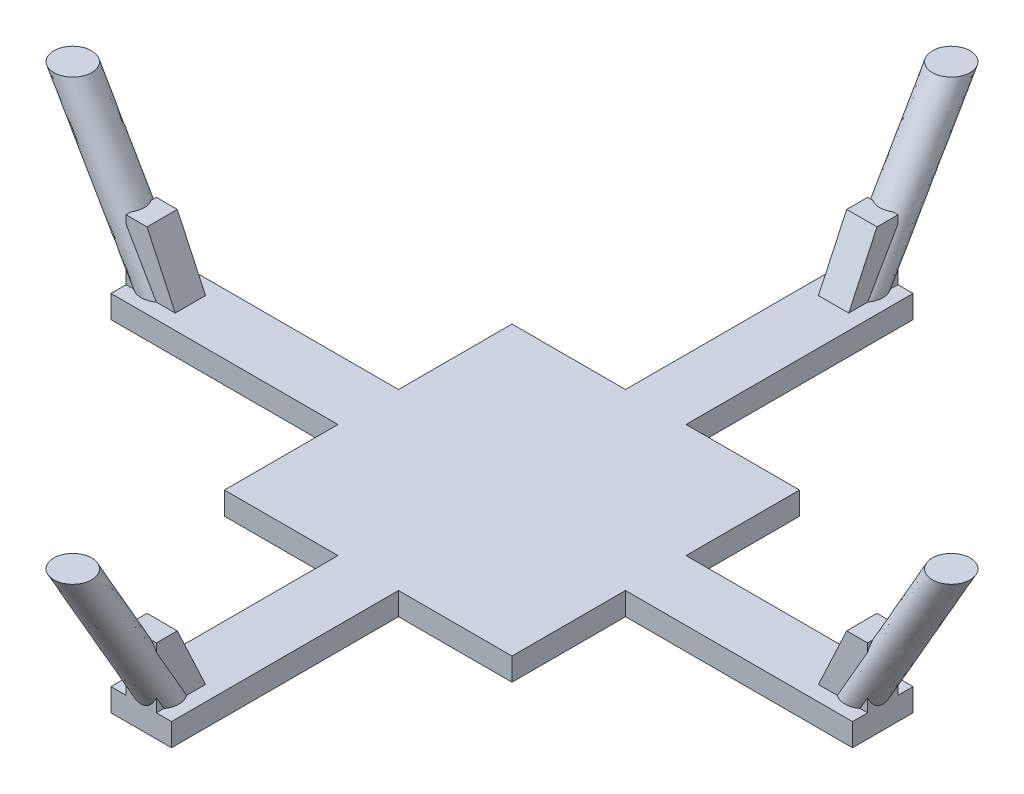
SolidWorks part; units mm, degrees
ref_plane "Front Plane" through (0, 0, 0) normal (0, 0, 1) x (1, 0, 0)
ref_plane "Top Plane" through (0, 0, 0) normal (0, 1, 0) x (1, 0, 0)
ref_plane "Right Plane" through (0, 0, 0) normal (1, 0, 0) x (0, 0, -1)
sketch "Sketch1" plane through (0, 0, 0) normal (0, 1, 0) x (1, 0, 0)
  line L1 (19, -19) -> (-19, -19)
  line L2 (19, -19) -> (19, 19)
  line L3 (19, 19) -> (-19, 19)
  line L4 (-19, -19) -> (-19, 19)
  line L5 (19, -19) -> (-19, 19) construction
  line L6 (19, 19) -> (-19, -19) construction
  point P0 (0, 0)
  dimension "D1" = 38
extrude "Boss-Extrude1" add sketch "Sketch1" along normal blind 3
sketch "Sketch2" plane through (0, 0, 0) normal (0, 1, 0) x (1, 0, 0)
  line L0 (-19, 4) -> (-49, 4)
  line L1 (-19, 19) -> (-19, -19) construction
  line L2 (-49, 4) -> (-49, -4)
  line L3 (-49, -4) -> (-19, -4)
  line L4 (-19, 0) -> (-49, 0) construction
  line L5 (-19, 4) -> (-19, -4)
  dimension "D1" = 8
  dimension "D2" = 30
extrude "Boss-Extrude2" add sketch "Sketch2" along normal up to surface (3 mm away) up to face at (0, 3, 0)
ref_axis "Axis1" through (0, 0, 0) along (0, 1, 0)
sketch "Sketch3" plane through (0, 3, 0) normal (0, 1, 0) x (1, 0, 0)
  line L0 (-49, 4) -> (-49, -4) construction
  line L1 (0, 0) -> (-46.5, 0) construction
  circle A0 centre (-46.5, 0) radius 2.5
  dimension "D1" = 5
extrude "Boss-Extrude3" [suppressed] add sketch "Sketch3" along normal blind 20
sketch "Sketch7" plane through (0, 0, 0) normal (0, 0, 1) x (1, 0, 0)
  line L0 (-46.5, 23) -> (-46.5, 3) construction
  line L1 (-58.047, 23) -> (-46.5, 23) construction
  line L2 (-46.5, 3) -> (0, 3) construction
  line L3 (-46.5, 3) -> (-58.047, 23)
  dimension "D1" = 30
  dimension "D2" = 46.5
  dimension "D3" = 20
  dimension "D4" = 3
sketch "Sketch8" plane through (0, 3, 0) normal (0, 1, 0) x (1, 0, 0)
  line L0 (-49, 4) -> (-49, -4) construction
  circle A0 centre (-46.5, 0) radius 2.5
sweep "Sweep1" add profiles "Sketch8" path "Sketch7"
sketch "Sketch6" plane through (0, 0, 0) normal (0, 0, 1) x (1, 0, 0)
  line L2 (-46.2305, 11) -> (-42.5, 3)
  line L3 (-42.5, 3) -> (-46.5, 3)
  line L6 (-46.2305, 11) -> (-49, 11)
  line L7 (-49, 11) -> (-49, 3)
  line L8 (-49, 3) -> (-46.5, 3)
  dimension "D1" = 8
  dimension "D2" = 4
  dimension "D3" = 2.5
  dimension "D5" = 65
extrude "Boss-Extrude5" add sketch "Sketch6" along normal mid plane 4
pattern_circular "CirPattern1" count 4 over 360 about axis through (0, 0, 0) along (0, 1, 0) of "Boss-Extrude2", "Boss-Extrude5", "Sweep1"
